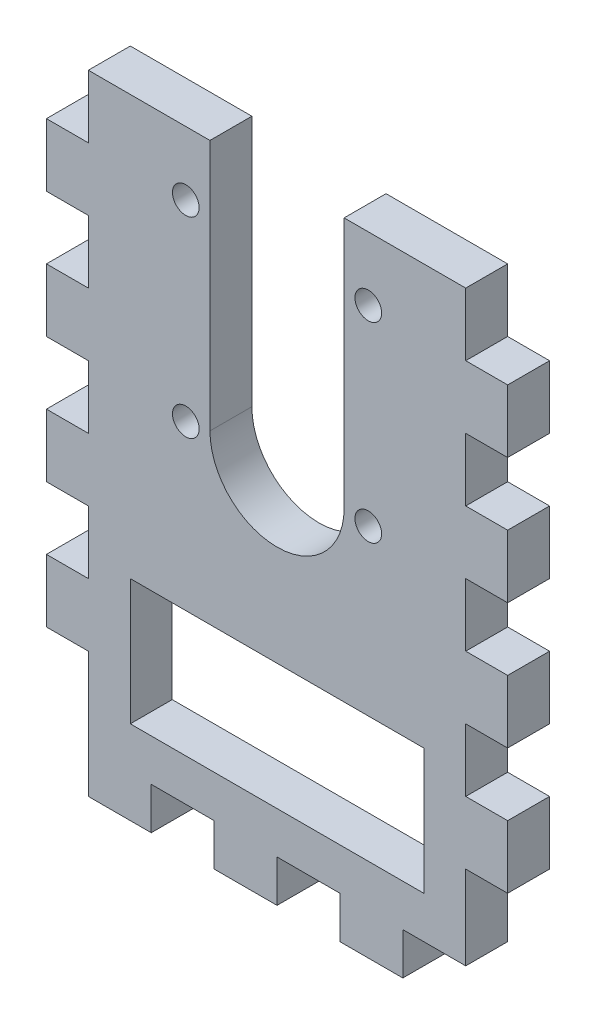
SolidWorks part; units mm, degrees
material "Pine"
ref_plane "Front Plane" through (0, 0, 0) normal (0, 0, 1) x (1, 0, 0)
ref_plane "Top Plane" through (0, 0, 0) normal (0, 1, 0) x (1, 0, 0)
ref_plane "Right Plane" through (0, 0, 0) normal (1, 0, 0) x (0, 0, -1)
sketch "Sketch1" plane through (0, 0, 0) normal (0, 0, 1) x (1, 0, 0)
  line L1 (0, 0) -> (57.15, 0)
  line L2 (0, 0) -> (0, -88.9)
  line L3 (0, -88.9) -> (57.15, -88.9)
  line L4 (57.15, 0) -> (57.15, -88.9)
  dimension "D1" = 88.9
  dimension "D2" = 57.15
extrude "Boss-Extrude1" add sketch "Sketch1" along normal blind 6.35
sketch "Sketch2" plane through (0, 0, 6.35) normal (0, 0, 1) x (1, 0, 0)
  line L0 (28.575, 0) -> (28.575, -38.1) construction
  line L1 (38.735, 0) -> (38.735, -38.1)
  line L2 (18.415, 0) -> (18.415, -38.1)
  line L3 (0, -88.9) -> (57.15, -88.9) construction
  line L4 (57.15, 0) -> (0, 0) construction
  line L5 (6.35, -63.5) -> (50.8, -63.5)
  line L6 (6.35, -63.5) -> (6.35, -82.55)
  line L7 (6.35, -82.55) -> (50.8, -82.55)
  line L8 (50.8, -63.5) -> (50.8, -82.55)
  line L9 (0, 0) -> (0, -88.9) construction
  arc A0 (38.735, 0) -> (18.415, 0) centre (28.575, 0) ccw
  arc A1 (18.415, -38.1) -> (38.735, -38.1) centre (28.575, -38.1) ccw
  circle A2 centre (42.3926, -9.652) radius 2.0193
  circle A3 centre (42.3926, -38.608) radius 2.0193
  circle A4 centre (14.7574, -38.6842) radius 2.0193
  circle A5 centre (14.7574, -9.652) radius 2.0193
  point P2 (28.575, -19.05)
  point P7 (28.575, -48.26)
  dimension "D2" = 10.16
  dimension "D3" = 4.0386
  dimension "D5" = 9.652
  dimension "D6" = 13.8176
  dimension "D7" = 13.8176
  dimension "D8" = 9.652
  dimension "D9" = 28.956
  dimension "D10" = 4.0386
  dimension "D11" = 4.0386
  dimension "D12" = 4.0386
  dimension "D1" = 48.26
  dimension "D4" = 29.0322
  dimension "D13" = 44.45
  dimension "D14" = 19.05
  dimension "D15" = 6.35
  dimension "D16" = 6.35
extrude "Cut-Extrude1" cut sketch "Sketch2" against normal up to surface (6.35 mm away) up to face at (28.575, -44.45, 0)
sketch "Sketch3" plane through (0, 0, 0) normal (0, 0, 1) x (1, 0, 0)
  line L1 (0, -9.525) -> (-6.35, -9.525)
  line L2 (0, -9.525) -> (0, -19.05)
  line L3 (0, -19.05) -> (-6.35, -19.05)
  line L4 (-6.35, -9.525) -> (-6.35, -19.05)
  line L5 (57.15, -88.9) -> (57.15, 0) construction
  line L6 (0, -28.575) -> (0, -38.1)
  line L7 (0, -28.575) -> (-6.35, -28.575)
  line L8 (-6.35, -28.575) -> (-6.35, -38.1)
  line L9 (0, -38.1) -> (-6.35, -38.1)
  line L10 (0, -47.625) -> (0, -57.15)
  line L11 (0, -47.625) -> (-6.35, -47.625)
  line L12 (-6.35, -47.625) -> (-6.35, -57.15)
  line L13 (0, -57.15) -> (-6.35, -57.15)
  line L14 (0, -66.675) -> (0, -76.2)
  line L15 (0, -66.675) -> (-6.35, -66.675)
  line L16 (-6.35, -66.675) -> (-6.35, -76.2)
  line L17 (0, -76.2) -> (-6.35, -76.2)
  line L23 (0, -88.9) -> (9.525, -88.9)
  line L24 (0, -88.9) -> (0, -95.25)
  line L25 (0, -95.25) -> (9.525, -95.25)
  line L26 (9.525, -88.9) -> (9.525, -95.25)
  line L39 (28.575, 0) -> (28.575, -88.9) construction
  line L40 (57.15, -66.675) -> (63.5, -66.675)
  line L41 (63.5, -66.675) -> (63.5, -76.2)
  line L42 (57.15, -76.2) -> (63.5, -76.2)
  line L43 (57.15, -66.675) -> (57.15, -76.2)
  line L44 (57.15, -47.625) -> (63.5, -47.625)
  line L45 (63.5, -47.625) -> (63.5, -57.15)
  line L46 (57.15, -57.15) -> (63.5, -57.15)
  line L47 (57.15, -47.625) -> (57.15, -57.15)
  line L48 (57.15, -28.575) -> (63.5, -28.575)
  line L49 (63.5, -28.575) -> (63.5, -38.1)
  line L50 (57.15, -38.1) -> (63.5, -38.1)
  line L51 (57.15, -28.575) -> (57.15, -38.1)
  line L52 (57.15, -19.05) -> (63.5, -19.05)
  line L53 (63.5, -9.525) -> (63.5, -19.05)
  line L54 (57.15, -9.525) -> (63.5, -9.525)
  line L55 (57.15, -9.525) -> (57.15, -19.05)
  line L56 (0, 0) -> (0, -88.9) construction
  line L57 (18.415, 0) -> (0, 0) construction
  line L59 (0, 0) -> (0, -88.9) construction
  line L61 (19.05, -88.9) -> (19.05, -95.25)
  line L62 (19.05, -88.9) -> (28.575, -88.9)
  line L63 (28.575, -88.9) -> (28.575, -95.25)
  line L64 (19.05, -95.25) -> (28.575, -95.25)
  line L65 (38.1, -88.9) -> (38.1, -95.25)
  line L66 (38.1, -88.9) -> (47.625, -88.9)
  line L67 (47.625, -88.9) -> (47.625, -95.25)
  line L68 (38.1, -95.25) -> (47.625, -95.25)
  line L69 (0, -88.9) -> (57.15, -88.9) construction
  dimension "D1" = 6.35
  dimension "D2" = 9.525
  dimension "D3" = 9.525
  dimension "D5" = 9.525
  dimension "D6" = 6.35
  dimension "D7" = 3
  dimension "D8" = 9.525
  dimension "D9" = 9.525
  dimension "D4" = 4
extrude "Boss-Extrude3" add sketch "Sketch3" along normal up to surface (6.35 mm away) up to face at (12.7381, -38.6842, 6.35)
